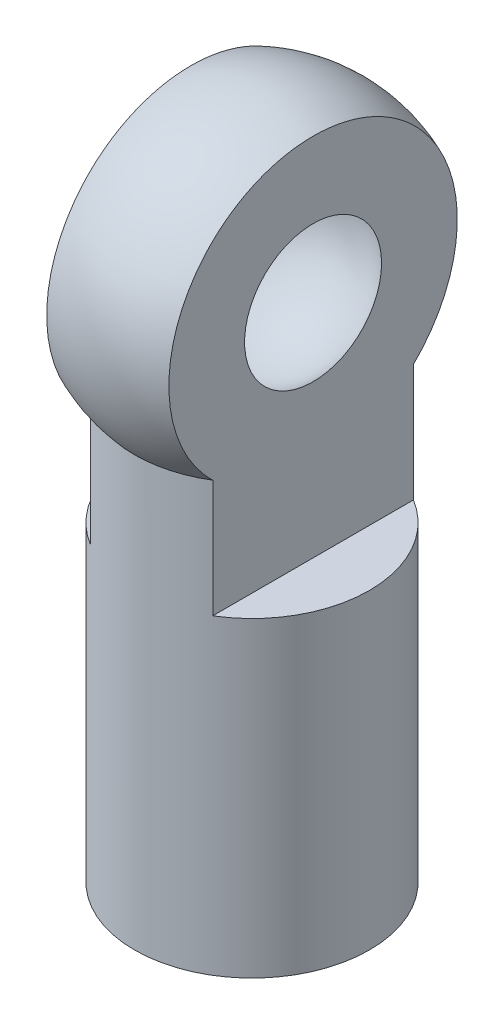
SolidWorks part; units mm, degrees
ref_plane "Front" through (0, 0, 0) normal (0, 0, 1) x (1, 0, 0)
ref_plane "Top" through (0, 0, 0) normal (0, 1, 0) x (1, 0, 0)
ref_plane "Right" through (0, 0, 0) normal (1, 0, 0) x (0, 0, -1)
sketch "Sketch4" plane through (0, 0, 0) normal (0, 0, 1) x (1, 0, 0)
  line L0 (0, -55) -> (0, 55) construction
  line L1 (0, 0) -> (3.75, 0)
  line L2 (0, 0) -> (0, 13.6928)
  line L4 (3.75, 0) -> (3.75, 13.6928)
  line L5 (0, 22) -> (0, 13.6928)
  line L6 (0, 26.7886) -> (0, -3.0568) construction
  arc A0 (0, 14.07) -> (0, 19.93) centre (0, 17) ccw
  arc A1 (3.75, 13.6928) -> (0, 22) centre (0, 17) ccw
  dimension "D1" = 10
  dimension "D2" = 5.86
  dimension "D4" = 17
  dimension "D3" = 3.75
revolve "Revolve2" add sketch "Sketch4" angle 360 about L6
ref_plane "Plane1" through (3.75, 0, 0) normal (1, 0, 0) x (0, 0, -1)
sketch "Sketch5" plane through (3.75, 0, 0) normal (1, 0, 0) x (0, 0, -1)
  line L1 (0, 5.5) -> (0, -5.5) construction
  line L2 (5.5, 0) -> (-5.5, 0) construction
  line L3 (-3.75, 13.6928) -> (-3.75, 0) construction
  line L4 (-3.75, 9.9428) -> (3.75, 9.9428)
  line L5 (-3.75, 9.9428) -> (-3.75, 13.6928)
  line L7 (3.75, 9.9428) -> (3.75, 13.6928)
  line L8 (3.75, 0) -> (3.75, 13.6928) construction
  arc A1 (3.75, 13.6928) -> (-3.75, 13.6928) centre (0, 17) ccw
  dimension "D1" = 10
  dimension "D2" = 17
  dimension "D3" = 3.75
extrude "Cut-Extrude1" cut sketch "Sketch5" against normal blind 1.8 and the other way through all
mirror "Mirror2" about plane through (0, 0, 0) normal (1, 0, 0) of "Cut-Extrude1"
sketch "Sketch6" plane through (0, 0, 0) normal (0, -1, 0) x (1, 0, 0)
  circle A0 centre (0, 0) radius 1.5
  dimension "D1" = 3
extrude "Cut-Extrude2" cut sketch "Sketch6" against normal blind 10 and the other way through all
